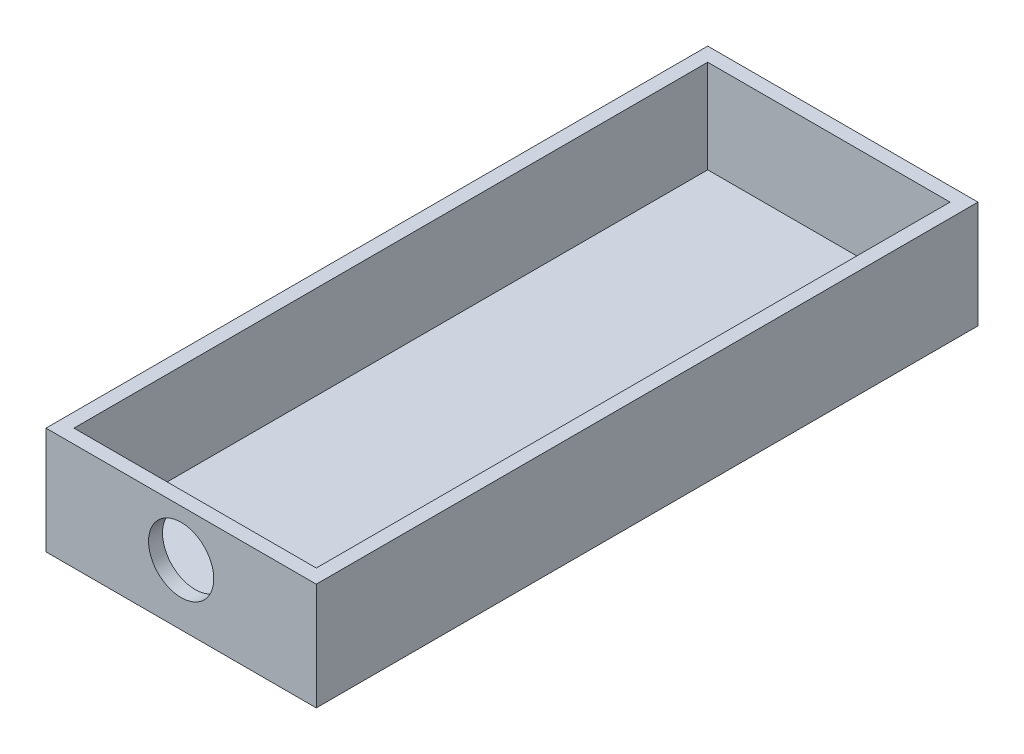
SolidWorks part; units mm, degrees
ref_plane "Front" through (0, 0, 0) normal (0, 0, 1) x (1, 0, 0)
ref_plane "Top" through (0, 0, 0) normal (0, 1, 0) x (1, 0, 0)
ref_plane "Right" through (0, 0, 0) normal (1, 0, 0) x (0, 0, -1)
sketch "Sketch1" plane through (0, 0, 0) normal (0, 1, 0) x (1, 0, 0)
  line L1 (0, 0) -> (29, 0)
  line L2 (0, 0) -> (0, 71)
  line L3 (0, 71) -> (29, 71)
  line L4 (29, 0) -> (29, 71)
  line L5 (0, 0) -> (29, 71) construction
  line L6 (0, 71) -> (29, 0) construction
  point P4 (14.5, 35.5)
  dimension "D1" = 71
  dimension "D2" = 29
extrude "Boss-Extrude1" add sketch "Sketch1" along normal blind 1.5
sketch "Sketch2" plane through (0, 1.5, 0) normal (0, 1, 0) x (1, 0, 0)
  line L4 (0, 71) -> (0, 0)
  line L5 (0, 0) -> (29, 0)
  line L6 (29, 0) -> (29, 71)
  line L7 (29, 71) -> (0, 71)
  line L8 (0, 71) -> (0, 0)
  line L9 (0, 0) -> (29, 0)
  line L10 (29, 0) -> (29, 71)
  line L11 (29, 71) -> (0, 71)
  line L16 (1.5, 69.5) -> (1.5, 1.5)
  line L17 (1.5, 1.5) -> (27.5, 1.5)
  line L18 (27.5, 1.5) -> (27.5, 69.5)
  line L19 (27.5, 69.5) -> (1.5, 69.5)
  line L20 (1.5, 69.5) -> (1.5, 1.5)
  line L21 (1.5, 1.5) -> (27.5, 1.5)
  line L22 (27.5, 1.5) -> (27.5, 69.5)
  line L23 (27.5, 69.5) -> (1.5, 69.5)
  dimension "D1" = 0
  dimension "D2" = 1.5
extrude "Boss-Extrude2" add sketch "Sketch2" along normal blind 10
sketch "Sketch3" plane through (0, 0, -1.5) normal (0, 0, -1) x (-1, 0, 0)
  line L0 (-27.5, 11.5) -> (-1.5, 1.5) construction
  circle A0 centre (-14.5, 6.5) radius 3.5
extrude "Cut-Extrude1" cut sketch "Sketch3" against normal blind 9
